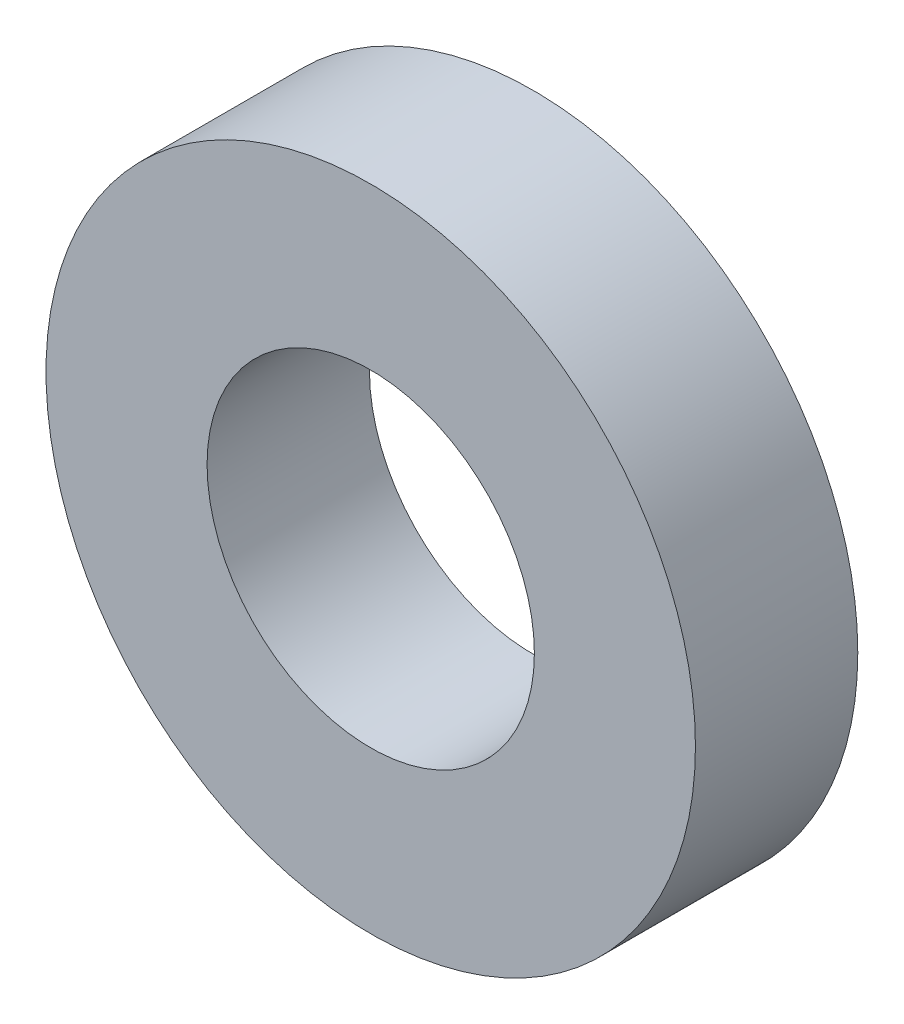
SolidWorks part; units mm, degrees
material "Alloy Steel"
ref_plane "Front Plane" through (0, 0, 0) normal (0, 0, 1) x (1, 0, 0)
ref_plane "Top Plane" through (0, 0, 0) normal (0, 1, 0) x (1, 0, 0)
ref_plane "Right Plane" through (0, 0, 0) normal (1, 0, 0) x (0, 0, -1)
sketch "Sketch1" plane through (0, 0, 0) normal (0, 0, 1) x (1, 0, 0)
  circle A0 centre (0, 0) radius 6.35
  circle A1 centre (0, 0) radius 3.2004
  dimension "OD" = 12.7
  dimension "ID" = 6.4008
extrude "Extrude1" add sketch "Sketch1" along normal mid plane 3.175
sketch "Sketch2" plane through (0, 0, 0) normal (1, 0, 0) x (0, 0, -1)
  line L0 (-1.5875, -3.2004) -> (1.5875, -3.2004) construction
  line L3 (1.5875, 3.2004) -> (-1.5875, 3.2004) construction
  line L5 (-1.5875, -3.2004) -> (1.5875, -3.2004)
  line L6 (1.5875, 3.2004) -> (-1.5875, 3.2004)
sketch "Sketch4" plane through (0, 0, 1.5875) normal (0, 0, 1) x (1, 0, 0)
  line L0 (0, 0) -> (-2.263, 2.263)
  line L1 (0, -2.1828) -> (0, 2.1828) construction
  circle A0 centre (0, 0) radius 3.2004 construction
  dimension "D1" = 45
